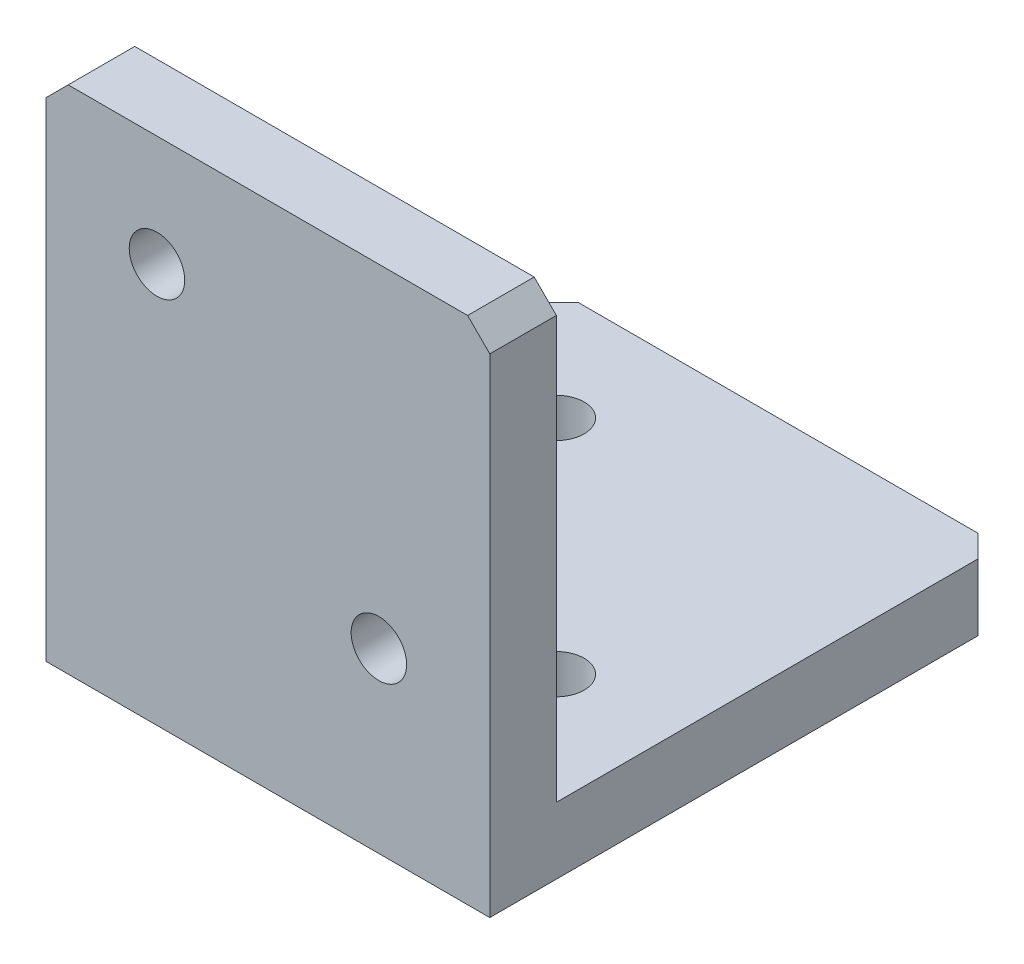
SolidWorks part; units mm, degrees
ref_plane "前视基准面" through (0, 0, 0) normal (0, 0, 1) x (1, 0, 0)
ref_plane "上视基准面" through (0, 0, 0) normal (0, 1, 0) x (1, 0, 0)
ref_plane "右视基准面" through (0, 0, 0) normal (1, 0, 0) x (0, 0, -1)
sketch "草图1" plane through (0, 0, 0) normal (0, 0, 1) x (1, 0, 0)
  line L1 (10, -10) -> (-10, -10)
  line L2 (10, -10) -> (10, 10)
  line L3 (10, 10) -> (-10, 10)
  line L4 (-10, -10) -> (-10, 10)
  line L5 (10, -10) -> (-10, 10) construction
  line L6 (10, 10) -> (-10, -10) construction
  point P0 (0, 0)
  dimension "D1" = 20
  dimension "D2" = 20
extrude "凸台-拉伸1" add sketch "草图1" along normal blind 3
sketch "草图2" plane through (0, 0, 3) normal (0, 0, 1) x (1, 0, 0)
  line L0 (10, -10) -> (10, 10) construction
  line L1 (-10, -10) -> (10, -10)
  line L2 (-10, -10) -> (-10, -13)
  line L3 (-10, -13) -> (10, -13)
  line L4 (10, -10) -> (10, -13)
  dimension "D1" = 3
extrude "凸台-拉伸2" add sketch "草图2" against normal blind 23
hole_wizard "M3 螺纹孔1" positions "草图4" profile "草图5" tap size "M3" standard "GB"
sketch "草图4" plane through (0, 0, 0) normal (0, 0, -1) x (-1, 0, 0)
  line L0 (10, 10) -> (10, -10) construction
  line L2 (-10, 10) -> (10, 10) construction
  line L3 (-10, -10) -> (10, -10) construction
  line L4 (-10, -10) -> (-10, 10) construction
  point P0 (5, 5)
  point P2 (-5, -5)
  dimension "D1" = 5
  dimension "D2" = 5
  dimension "D3" = 5
  dimension "D4" = 5
sketch "草图5" plane through (-5, 5, 0) normal (1, 0, 0) x (0, 1, 0)
  line L0 (0, 0) -> (0, 8.2511)
  line L1 (0, 8.2511) -> (1.25, 7.5)
  line L2 (1.25, 7.5) -> (1.25, 0)
  line L5 (1.25, 0) -> (0, 0)
  line L10 (0, 8.2511) -> (-1.25, 7.5) construction
  line L11 (0, -6.35) -> (0, 107.95) construction
  dimension "螺纹孔钻头直径" = 2.5
  dimension "螺纹孔钻头深度" = 7.5
  dimension "导头角度" = 118
cosmetic thread "孔螺蚊线1"
cosmetic thread "孔螺蚊线2"
hole_wizard "M3 螺纹孔2" positions "草图6" profile "草图7" tap size "M3" standard "GB"
sketch "草图6" plane through (0, -10, 0) normal (0, 1, 0) x (1, 0, 0)
  line L0 (10, 20) -> (-10, 20) construction
  line L1 (-10, 20) -> (-10, 0) construction
  line L2 (10, 20) -> (10, 0) construction
  line L3 (-10, 0) -> (10, 0) construction
  point P0 (-5, 15)
  point P2 (5, 5)
  dimension "D1" = 5
  dimension "D2" = 5
  dimension "D3" = 5
  dimension "D4" = 5
sketch "草图7" plane through (-5, -10, -15) normal (1, 0, 0) x (0, 0, 1)
  line L0 (0, 0) -> (0, 8.2511)
  line L1 (0, 8.2511) -> (1.25, 7.5)
  line L2 (1.25, 7.5) -> (1.25, 0)
  line L5 (1.25, 0) -> (0, 0)
  line L10 (0, 8.2511) -> (-1.25, 7.5) construction
  line L11 (0, -6.35) -> (0, 107.95) construction
  dimension "螺纹孔钻头直径" = 2.5
  dimension "螺纹孔钻头深度" = 7.5
  dimension "导头角度" = 118
cosmetic thread "孔螺蚊线3"
cosmetic thread "孔螺蚊线4"
chamfer "倒角1" distance 1 angle 45 4 edges at (-10, -11.5, -20) (10, -11.5, -20) (-10, 10, 1.5) (10, 10, 1.5)
